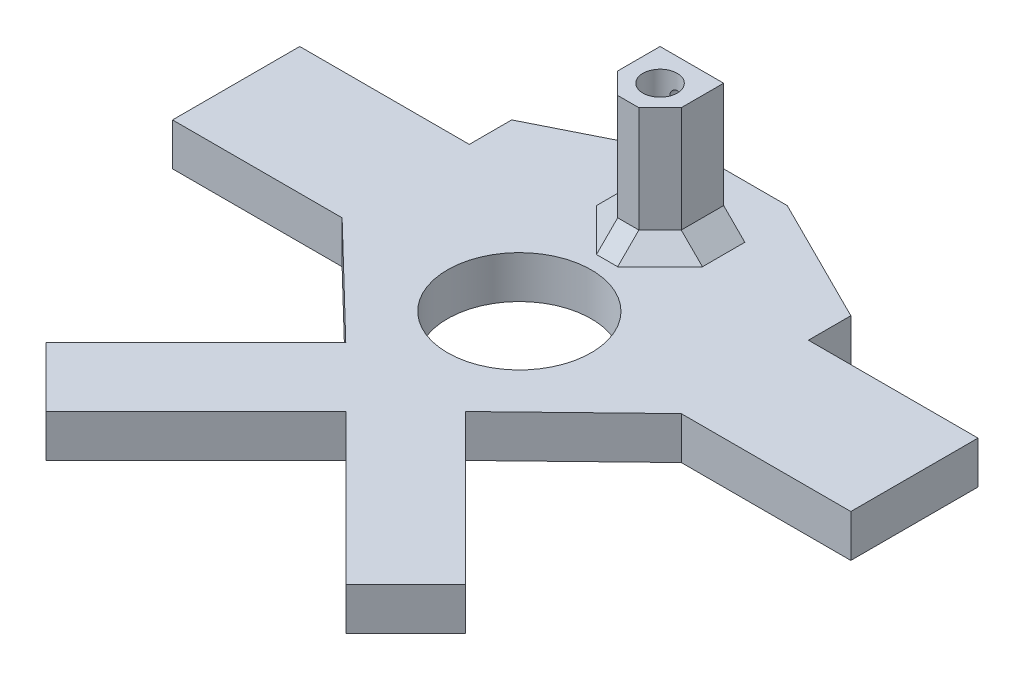
SolidWorks part; units mm, degrees
ref_plane "Ebene vorne" through (0, 0, 0) normal (0, 0, 1) x (1, 0, 0)
ref_plane "Ebene oben" through (0, 0, 0) normal (0, 1, 0) x (1, 0, 0)
ref_plane "Ebene rechts" through (0, 0, 0) normal (1, 0, 0) x (0, 0, -1)
sketch "Sketch1" plane through (0, 0, 0) normal (0, 1, 0) x (1, 0, 0)
  line L0 (-40, 0) -> (-80, 0) construction
  line L1 (-40, 40) -> (40, 40)
  line L2 (-40, 40) -> (-40, -40)
  line L3 (-40, -40) -> (40, -40)
  line L4 (40, 40) -> (40, -40)
  line L5 (-40, 40) -> (40, -40) construction
  line L6 (-40, -40) -> (40, 40) construction
  line L7 (0, 40) -> (0, -40) construction
  line L8 (-40, -15) -> (-80, -15)
  line L9 (-40, -15) -> (-40, 15)
  line L10 (-40, 15) -> (-80, 15)
  line L11 (-80, -15) -> (-80, 15)
  line L12 (-40, -15) -> (-80, 15) construction
  line L13 (-40, 15) -> (-80, -15) construction
  line L14 (40, 15) -> (80, -15) construction
  line L15 (40, -15) -> (80, 15) construction
  line L16 (40, 0) -> (80, 0) construction
  line L17 (80, -15) -> (80, 15)
  line L18 (40, 15) -> (80, 15)
  line L19 (40, -15) -> (40, 15)
  line L20 (40, -15) -> (80, -15)
  line L21 (0, -40) -> (-42.4264, -82.4264) construction
  line L22 (0, -40) -> (42.4264, -82.4264) construction
  line L23 (-7.0711, -32.9289) -> (-49.4975, -75.3553)
  line L24 (-7.0711, -32.9289) -> (7.0711, -47.0711)
  line L25 (-49.4975, -75.3553) -> (-35.3553, -89.4975)
  line L26 (7.0711, -47.0711) -> (-35.3553, -89.4975)
  line L27 (-7.0711, -32.9289) -> (-35.3553, -89.4975) construction
  line L28 (-49.4975, -75.3553) -> (7.0711, -47.0711) construction
  line L29 (7.0711, -32.9289) -> (49.4975, -75.3553)
  line L30 (7.0711, -32.9289) -> (-7.0711, -47.0711)
  line L31 (49.4975, -75.3553) -> (35.3553, -89.4975)
  line L32 (-7.0711, -47.0711) -> (35.3553, -89.4975)
  line L33 (7.0711, -32.9289) -> (35.3553, -89.4975) construction
  line L34 (49.4975, -75.3553) -> (-7.0711, -47.0711) construction
  line L35 (-40, -15) -> (-14.1421, -40)
  line L36 (40, -15) -> (14.1421, -40)
  line L37 (-40, 25) -> (-10, 40)
  line L38 (10, 40) -> (40, 25)
  point P0 (0, 0)
  point P8 (-60, 0)
  point P21 (60, 0)
  point P25 (-21.2132, -61.2132)
  point P26 (21.2132, -61.2132)
  point P31 (21.2132, -61.2132)
  point P36 (-21.2132, -61.2132)
  dimension "D1" = 80
  dimension "D2" = 80
  dimension "D3" = 40
  dimension "D4" = 30
  dimension "D5" = 45
  dimension "D6" = 45
  dimension "D7" = 60
  dimension "D8" = 60
  dimension "D9" = 20
  dimension "D10" = 20
  dimension "D11" = 10
  dimension "D12" = 30
  dimension "D13" = 10
  dimension "D14" = 30
extrude "Boss-Extrude1" add sketch "Sketch1" along normal blind 10 contours L26 L32 L31 L29 L3 L24 | L30 L32 L26 L24 | L32 L30 L3 L23 L25 L26 | L38 L1 L37 L2 L35 L23 L24 L30 L29 L36 L4 | L29 L30 L3 | L24 L23 L3 | L11 L8 L2 L10 | L4 L20 L17 L18
sketch "Sketch2" plane through (0, 10, 0) normal (0, 1, 0) x (1, 0, 0)
  line L0 (0, 0) -> (0, 40) construction
  line L1 (-10, 40) -> (10, 40) construction
  circle A0 centre (0, 20) radius 4.05
  dimension "D1" = 8.1
  dimension "D2" = 20
extrude "Cut-Extrude1" cut sketch "Sketch2" against normal blind 10
sketch "Sketch3" plane through (0, 10, 0) normal (0, 1, 0) x (1, 0, 0)
  line L1 (-7.5, 27.5) -> (7.5, 27.5)
  line L2 (-7.5, 27.5) -> (-7.5, 12.5)
  line L3 (-7.5, 12.5) -> (7.5, 12.5)
  line L4 (7.5, 27.5) -> (7.5, 12.5)
  line L5 (-7.5, 27.5) -> (7.5, 12.5) construction
  line L6 (-7.5, 12.5) -> (7.5, 27.5) construction
  circle A0 centre (0, 20) radius 4.05 construction
  circle A1 centre (0, 20) radius 4.05
  dimension "D1" = 15
  dimension "D2" = 15
extrude "Boss-Extrude2" add sketch "Sketch3" along normal blind 30
sketch "Sketch4" plane through (0, 0, -27.5) normal (0, 0, -1) x (-1, 0, 0)
  line L0 (0, 40) -> (0, 10) construction
  line L1 (-7.5, 40) -> (7.5, 40) construction
  line L2 (-7.5, 10) -> (7.5, 10) construction
  circle A0 centre (0, 35) radius 1.45
  circle A1 centre (0, 20) radius 1.45
  dimension "D1" = 2.9
  dimension "D2" = 15
  dimension "D3" = 5
extrude "Cut-Extrude2" cut sketch "Sketch4" against normal blind 5
chamfer "Chamfer1" distance 5 angle 45 5 edges at (-7.5, 10, -20) (7.5, 10, -20) (-7.5, 25, -12.5) (0, 10, -12.5) (7.5, 25, -12.5)
sketch "Sketch5" plane through (0, 10, 0) normal (0, 1, 0) x (1, 0, 0)
  line L0 (0, -54.1421) -> (0, 7.5) construction
  line L1 (2.5, 7.5) -> (-2.5, 7.5) construction
  circle A0 centre (0, -13.1912) radius 16.957
extrude "Cut-Extrude3" cut sketch "Sketch5" against normal blind 10
